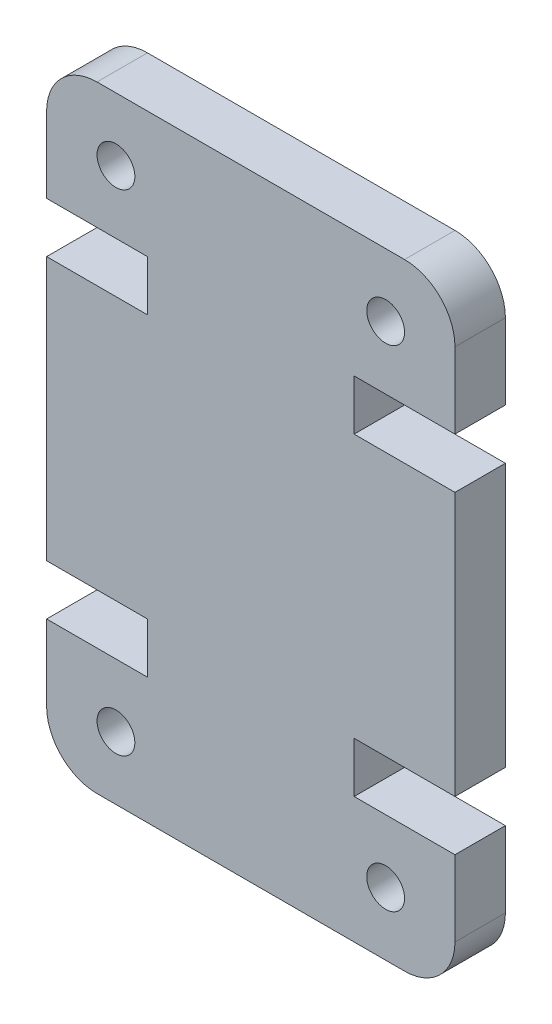
SolidWorks part; units mm, degrees
ref_plane "Front Plane" through (0, 0, 0) normal (0, 0, 1) x (1, 0, 0)
ref_plane "Top Plane" through (0, 0, 0) normal (0, 1, 0) x (1, 0, 0)
ref_plane "Right Plane" through (0, 0, 0) normal (1, 0, 0) x (0, 0, -1)
sketch "Sketch1" plane through (0, 0, 0) normal (0, 0, 1) x (1, 0, 0)
  line L0 (0, 17.45) -> (0, 7)
  line L1 (16.2, 5) -> (16.2, 2)
  line L2 (12.2, 5) -> (16.2, 5)
  line L3 (2, 0) -> (14.2, 0)
  line L4 (16.2, 7) -> (12.2, 7)
  line L5 (12.2, 7) -> (12.2, 5)
  line L6 (16.2, 17.45) -> (16.2, 7)
  line L7 (0, 19.45) -> (0, 22.45)
  line L8 (4, 19.45) -> (0, 19.45)
  line L9 (0, 17.45) -> (4, 17.45)
  line L10 (4, 7) -> (4, 5)
  line L11 (4, 17.45) -> (4, 19.45)
  line L12 (0, 7) -> (4, 7)
  line L13 (4, 5) -> (0, 5)
  line L14 (12.2, 17.45) -> (12.2, 19.45)
  line L15 (16.2, 17.45) -> (12.2, 17.45)
  line L16 (2, 24.45) -> (14.2, 24.45)
  line L17 (12.2, 19.45) -> (16.2, 19.45)
  line L18 (16.2, 19.45) -> (16.2, 22.45)
  line L19 (0, 5) -> (0, 2)
  line L20 (0, 12.225) -> (16.2, 12.225) construction
  line L21 (8.1, 24.45) -> (8.1, 0) construction
  circle A0 centre (13.45, 2.5) radius 0.75
  arc A1 (16.2, 2) -> (14.2, 0) centre (14.2, 2) cw
  circle A2 centre (2.75, 21.95) radius 0.75
  arc A3 (0, 2) -> (2, 0) centre (2, 2) ccw
  arc A4 (0, 22.45) -> (2, 24.45) centre (2, 22.45) cw
  circle A5 centre (2.75, 2.5) radius 0.75
  arc A6 (16.2, 22.45) -> (14.2, 24.45) centre (14.2, 22.45) ccw
  circle A7 centre (13.45, 21.95) radius 0.75
  point P17 (8.1, 12.225)
  dimension "D1" = 1.5
  dimension "D2" = 2
  dimension "D3" = 2.75
  dimension "D4" = 8.1
  dimension "D5" = 2.5
  dimension "D6" = 5
  dimension "D8" = 12.225
extrude "Boss-Extrude1" add sketch "Sketch1" along normal blind 2
equation "\"D4@Sketch1\"= \"fingerWidth@parametersSketch@prostheticParameters.SLDPRT\" / 2 'MIP Width"
equation "\"D8@Sketch1\"= ( ( \"HL@parametersSketch@prostheticParameters.SLDPRT\" * 0.17 ) - 4 - 3 ) / 2 'MIP Length - Sil. Sht MIP - Sil. Sht DIP"
